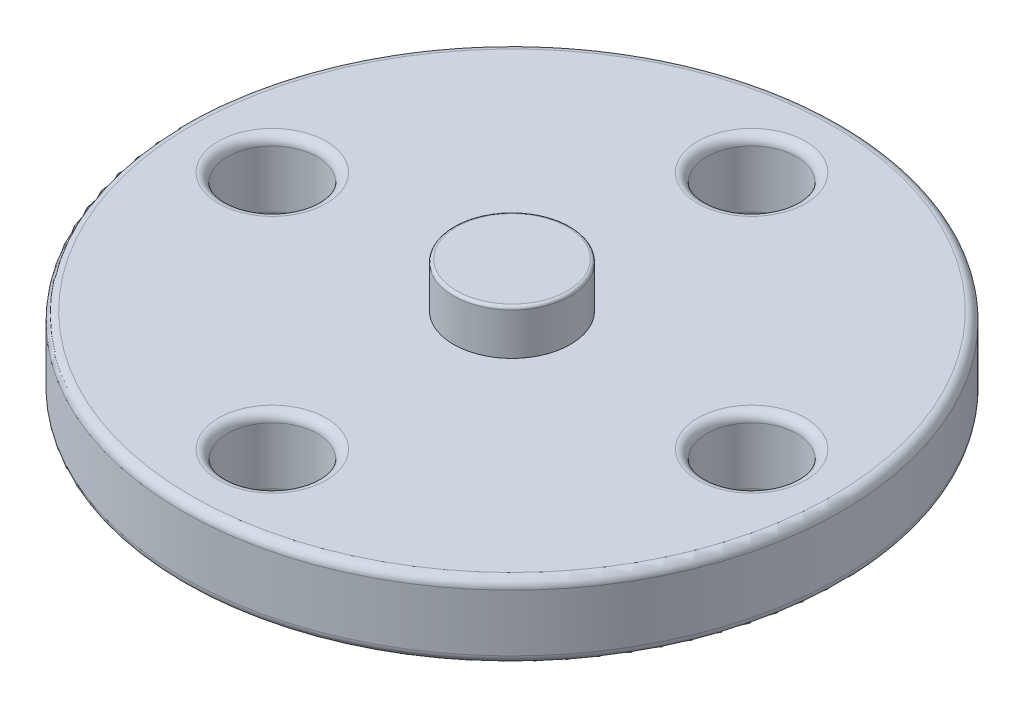
SolidWorks part; units mm, degrees
ref_plane "Front Plane" through (0, 0, 0) normal (0, 0, 1) x (1, 0, 0)
ref_plane "Top Plane" through (0, 0, 0) normal (0, 1, 0) x (1, 0, 0)
ref_plane "Right Plane" through (0, 0, 0) normal (1, 0, 0) x (0, 0, -1)
sketch "Sketch1" plane through (0, 0, 0) normal (0, 1, 0) x (1, 0, 0)
  line L0 (3, 47.4052) -> (0, 54.5)
  line L1 (0, 54.5) -> (-3, 47.4052)
  line L2 (0, 54.5) -> (0, 47.5) construction
  line L3 (-3, 47.4052) -> (0, 47.5) construction
  line L4 (0, 47.5) -> (3, 47.4052) construction
  line L5 (-3, 47.4052) -> (0, 47.5) construction
  line L6 (0, 47.5) -> (3, 47.4052) construction
  line L7 (13.8515, 45.4355) -> (12.5686, 53.0309)
  line L8 (12.5686, 53.0309) -> (8.0132, 46.8192)
  line L9 (23.9563, 41.0164) -> (24.4596, 48.703)
  line L10 (24.4596, 48.703) -> (18.5945, 43.7092)
  line L11 (32.7696, 34.3861) -> (35.0319, 41.7494)
  line L12 (35.0319, 41.7494) -> (28.1733, 38.2428)
  line L13 (39.8163, 25.902) -> (43.7157, 32.5451)
  line L14 (43.7157, 32.5451) -> (36.2333, 30.7148)
  line L15 (44.7164, 16.0216) -> (50.0428, 21.5863)
  line L16 (50.0428, 21.5863) -> (42.3399, 21.5309)
  line L17 (47.2059, 5.2774) -> (53.672, 9.4638)
  line L18 (53.672, 9.4638) -> (46.164, 11.1862)
  line L19 (47.1505, -5.7513) -> (54.4078, -3.1689)
  line L20 (54.4078, -3.1689) -> (47.4994, 0.2386)
  line L21 (44.5532, -16.4699) -> (52.2104, -15.6308)
  line L22 (52.2104, -15.6308) -> (46.2741, -10.722)
  line L23 (39.5541, -26.3007) -> (47.1984, -27.25)
  line L24 (47.1984, -27.25) -> (42.5541, -21.1045)
  line L25 (32.4225, -34.7135) -> (39.6419, -37.4002)
  line L26 (39.6419, -37.4002) -> (36.54, -30.3493)
  line L27 (23.5431, -41.255) -> (29.9482, -45.5341)
  line L28 (29.9482, -45.5341) -> (28.556, -37.9579)
  line L29 (13.3944, -45.5723) -> (18.6401, -51.2132)
  line L30 (18.6401, -51.2132) -> (19.0326, -43.5202)
  line L31 (2.5237, -47.4329) -> (6.3271, -54.1315)
  line L32 (6.3271, -54.1315) -> (8.4831, -46.7364)
  line L33 (-8.4831, -46.7364) -> (-6.3271, -54.1315)
  line L34 (-6.3271, -54.1315) -> (-2.5237, -47.4329)
  line L35 (-19.0326, -43.5202) -> (-18.6401, -51.2132)
  line L36 (-18.6401, -51.2132) -> (-13.3944, -45.5723)
  line L37 (-28.556, -37.9579) -> (-29.9482, -45.5341)
  line L38 (-29.9482, -45.5341) -> (-23.5431, -41.255)
  line L39 (-36.54, -30.3493) -> (-39.6419, -37.4002)
  line L40 (-39.6419, -37.4002) -> (-32.4225, -34.7135)
  line L41 (-42.5541, -21.1045) -> (-47.1984, -27.25)
  line L42 (-47.1984, -27.25) -> (-39.5541, -26.3007)
  line L43 (-46.2741, -10.722) -> (-52.2104, -15.6308)
  line L44 (-52.2104, -15.6308) -> (-44.5532, -16.4699)
  line L45 (-47.4994, 0.2386) -> (-54.4078, -3.1689)
  line L46 (-54.4078, -3.1689) -> (-47.1505, -5.7513)
  line L47 (-46.164, 11.1862) -> (-53.672, 9.4638)
  line L48 (-53.672, 9.4638) -> (-47.2059, 5.2774)
  line L49 (-42.3399, 21.5309) -> (-50.0428, 21.5863)
  line L50 (-50.0428, 21.5863) -> (-44.7164, 16.0216)
  line L51 (-36.2333, 30.7148) -> (-43.7157, 32.5451)
  line L52 (-43.7157, 32.5451) -> (-39.8163, 25.902)
  line L53 (-28.1733, 38.2428) -> (-35.0319, 41.7494)
  line L54 (-35.0319, 41.7494) -> (-32.7696, 34.3861)
  line L55 (-18.5945, 43.7092) -> (-24.4596, 48.703)
  line L56 (-24.4596, 48.703) -> (-23.9563, 41.0164)
  line L57 (-8.0132, 46.8192) -> (-12.5686, 53.0309)
  line L58 (-12.5686, 53.0309) -> (-13.8515, 45.4355)
  line L59 (0, 16) -> (0, 37.5) construction
  line L60 (-4.5, 37.229) -> (-4.5, 15.3542)
  line L61 (4.5, 37.229) -> (4.5, 15.3542)
  line L62 (37.229, -4.5) -> (15.3542, -4.5)
  line L63 (37.229, 4.5) -> (15.3542, 4.5)
  line L64 (-4.5, -37.229) -> (-4.5, -15.3542)
  line L65 (4.5, -37.229) -> (4.5, -15.3542)
  line L66 (-37.229, 4.5) -> (-15.3542, 4.5)
  line L67 (-37.229, -4.5) -> (-15.3542, -4.5)
  line L68 (0, 0) -> (0, 5.8384) construction
  line L70 (0, 0) -> (-4.8311, 0) construction
  line L71 (0, 0) -> (0, 5.8384) construction
  line L72 (0, 0) -> (-4.8311, 0) construction
  circle A0 centre (0, 0) radius 47.5
  circle A1 centre (0, 0) radius 37.5
  circle A2 centre (0, 0) radius 5
  circle A3 centre (0, 0) radius 2.2
  circle A4 centre (0, 0) radius 16
  circle A5 centre (0, 0) radius 46.5
  circle A6 centre (-8, 0) radius 1.5
  circle A7 centre (0, 8) radius 1.5
  circle A8 centre (8, 0) radius 1.5
  circle A9 centre (0, -8) radius 1.5
  circle A10 centre (-8, 0) radius 1.5
  circle A11 centre (0, 8) radius 1.5
  circle A12 centre (8, 0) radius 1.5
  circle A13 centre (0, -8) radius 1.5
  circle A15 centre (0, 0) radius 11
  point P88 (0, 0)
  point P111 (0, 0)
  point P123 (0, 0)
  point P135 (0, 0)
  dimension "D1" = 95
  dimension "D5" = 75
  dimension "D6" = 10
  dimension "D7" = 4.4
  dimension "D8" = 32
  dimension "D9" = 4
  dimension "D12" = 1
  dimension "D13" = 22
  dimension "D2" = 7
  dimension "D3" = 3
  dimension "D10" = 9
  dimension "D4" = 27
extrude "Boss-Extrude1" add sketch "Sketch1" along normal blind 2.5
fillet "Fillet1" radius 0.3 10 edges at (-8, 0, 1.5) (0, 0, -6.5) (8, 0, 1.5) (0, 0, 9.5) (0, 0, 11) (-8, 2.5, 1.5) (0, 2.5, -6.5) (8, 2.5, 1.5) (0, 2.5, 9.5) (0, 2.5, 11)
sketch "Sketch2" plane through (0, 2.5, 0) normal (0, 1, 0) x (1, 0, 0)
  circle A0 centre (0, 0) radius 1.95
  dimension "D1" = 3.9
extrude "Boss-Extrude2" add sketch "Sketch2" along normal blind 1.5
fillet "Fillet2" radius 0.1 1 edges at (0, 4, 1.95)
